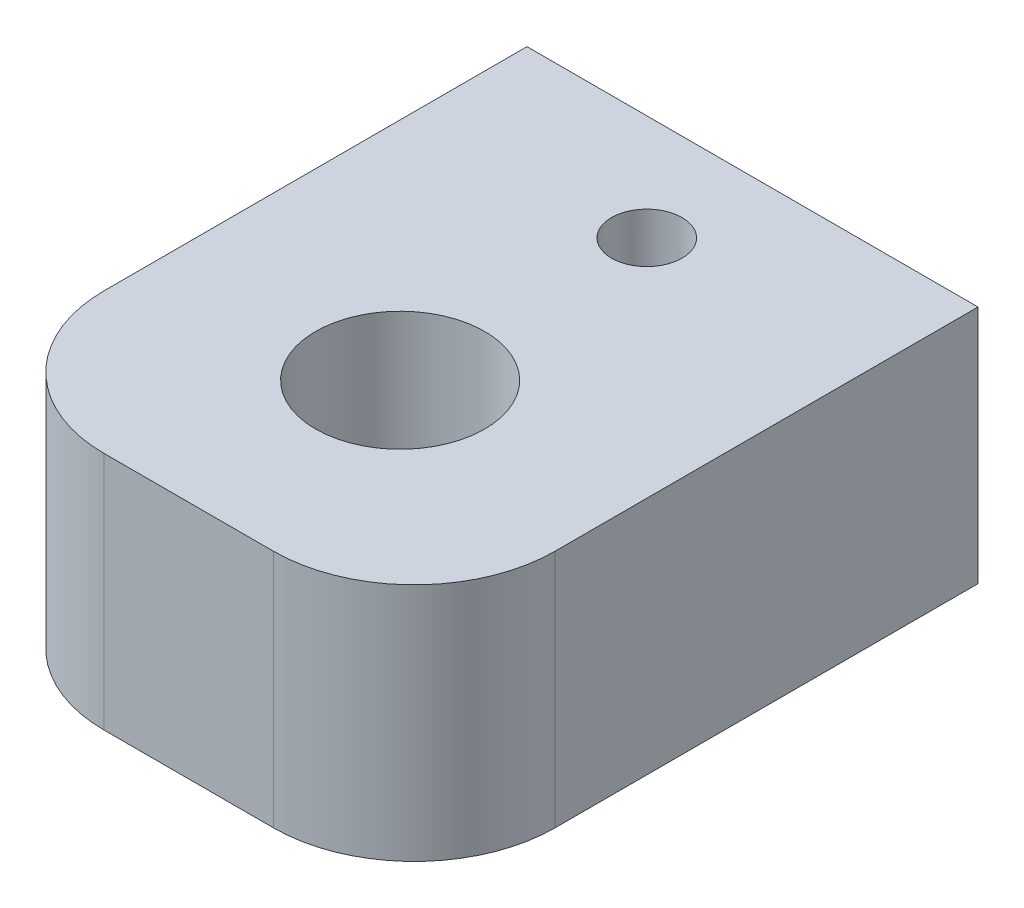
SolidWorks part; units mm, degrees
ref_plane "Front Plane" through (0, 0, 0) normal (0, 0, 1) x (1, 0, 0)
ref_plane "Top Plane" through (0, 0, 0) normal (0, 1, 0) x (1, 0, 0)
ref_plane "Right Plane" through (0, 0, 0) normal (1, 0, 0) x (0, 0, -1)
sketch "Sketch1" plane through (0, 0, 0) normal (0, 1, 0) x (1, 0, 0)
  line L0 (0, -20) -> (0, 20) construction
  line L1 (-16, 20) -> (16, 20)
  line L2 (-16, 20) -> (-16, -10)
  line L3 (-6, -20) -> (6, -20)
  line L4 (16, 20) -> (16, -10)
  line L5 (-16, 20) -> (16, -20) construction
  line L6 (-16, -20) -> (16, 20) construction
  arc A0 (16, -10) -> (6, -20) centre (6, -10) cw
  arc A1 (-6, -20) -> (-16, -10) centre (-6, -10) cw
  circle A2 centre (0, 12.5) radius 2.5
  circle A3 centre (0, -5) radius 6
  point P0 (0, 0)
  point P18 (0, 0)
  point P19 (0, 0)
  dimension "D3" = 10
  dimension "D4" = 5
  dimension "D5" = 12
  dimension "D1" = 32
  dimension "D2" = 40
  dimension "D6" = 7.5
  dimension "D7" = 15
extrude "Boss-Extrude1" add sketch "Sketch1" along normal blind 17
sketch "Sketch2" plane through (0, 0, -20) normal (0, 0, -1) x (-1, 0, 0)
  line L0 (0, 17) -> (0, 0) construction
  line L1 (-16, 17) -> (16, 17)
  line L2 (-16, 17) -> (-16, 0)
  line L3 (-16, 0) -> (16, 0)
  line L4 (16, 17) -> (16, 0)
  line L5 (-16, 8.5) -> (16, 8.5) construction
  circle A0 centre (0, 8.5) radius 5
  dimension "D1" = 10
extrude "Cut-Extrude1" cut sketch "Sketch2" against normal blind 15 contours A0
